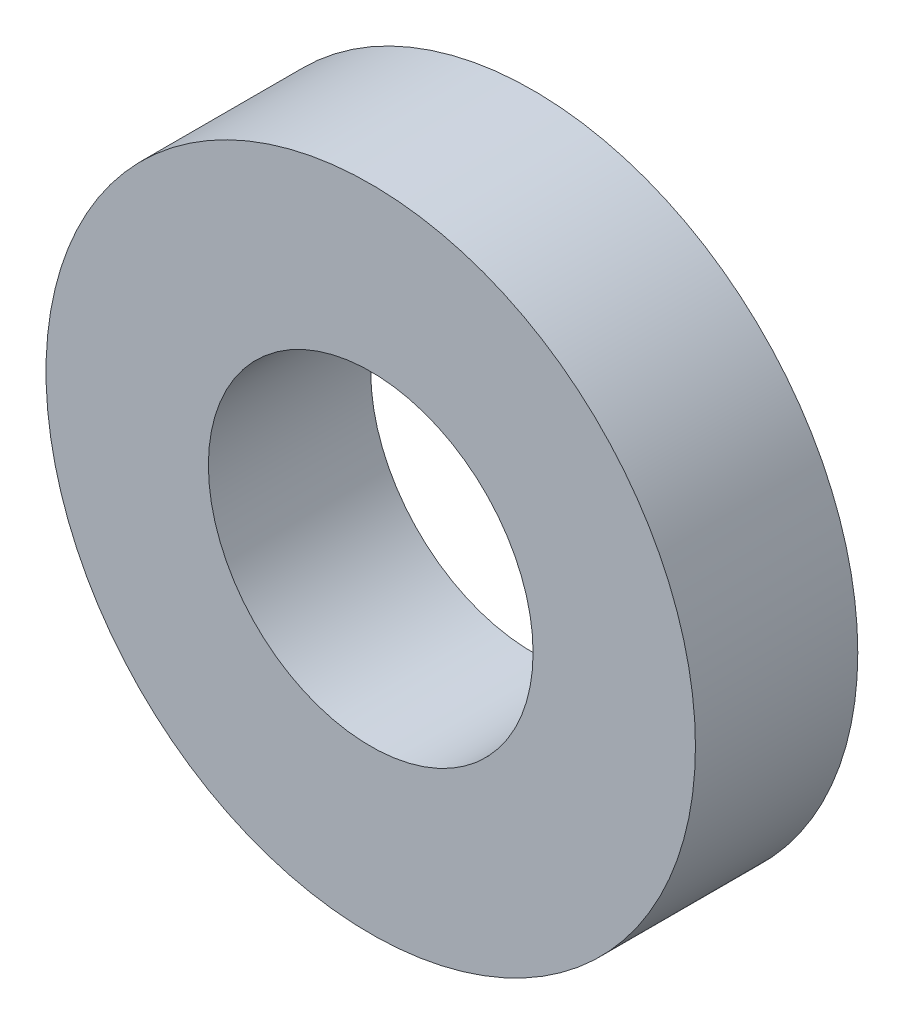
SolidWorks part; units mm, degrees
ref_plane "前视基准面" through (0, 0, 0) normal (0, 0, 1) x (1, 0, 0)
ref_plane "上视基准面" through (0, 0, 0) normal (0, 1, 0) x (1, 0, 0)
ref_plane "右视基准面" through (0, 0, 0) normal (1, 0, 0) x (0, 0, -1)
sketch "草图1" plane through (0, 0, 0) normal (0, 0, 1) x (1, 0, 0)
  circle A0 centre (0, 0) radius 10
  circle A1 centre (0, 0) radius 20
  dimension "D1" = 20
  dimension "D2" = 40
extrude "凸台-拉伸1" add sketch "草图1" along normal blind 10
